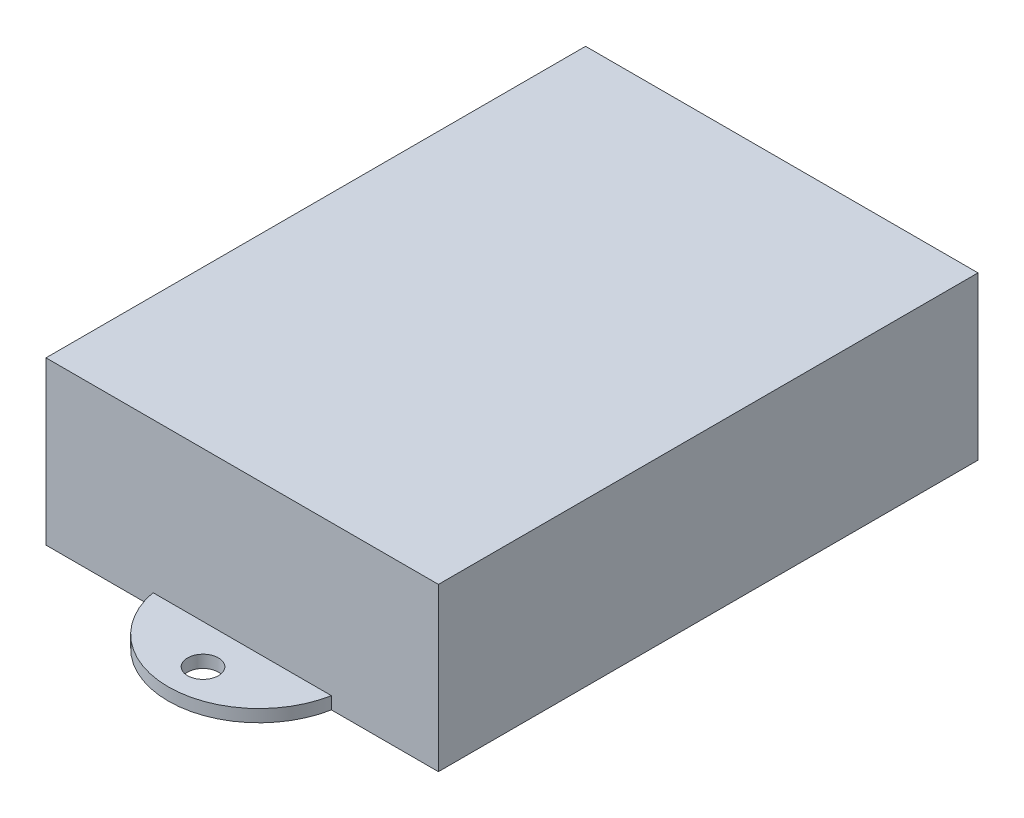
SolidWorks part; units mm, degrees
ref_plane "Front Plane" through (0, 0, 0) normal (0, 0, 1) x (1, 0, 0)
ref_plane "Top Plane" through (0, 0, 0) normal (0, 1, 0) x (1, 0, 0)
ref_plane "Right Plane" through (0, 0, 0) normal (1, 0, 0) x (0, 0, -1)
sketch "Sketch1" plane through (0, 0, 0) normal (0, 1, 0) x (1, 0, 0)
  line L1 (0, 0) -> (50.8, 0)
  line L2 (0, 0) -> (0, 69.85)
  line L3 (0, 69.85) -> (50.8, 69.85)
  line L4 (50.8, 0) -> (50.8, 69.85)
  dimension "D1" = 50.8
  dimension "D2" = 69.85
extrude "Boss-Extrude1" add sketch "Sketch1" along normal blind 21
sketch "Sketch2" plane through (0, 0, 0) normal (0, -1, 0) x (1, 0, 0)
  line L0 (25.4, 0) -> (25.4, -69.85) construction
  line L1 (0, 0) -> (50.8, 0) construction
  line L2 (50.8, -69.85) -> (0, -69.85) construction
  line L3 (25.4, -2.1787) -> (25.4, -67.6713) construction
  line L4 (37.1537, -2.1787) -> (37.1537, -67.6713)
  line L5 (13.6463, -2.1787) -> (13.6463, -67.6713)
  line L6 (25.4, 9.575) -> (25.4, -79.425) construction
  arc A0 (37.1537, -2.1787) -> (13.6463, -2.1787) centre (25.4, -2.1787) ccw
  arc A1 (13.6463, -67.6713) -> (37.1537, -67.6713) centre (25.4, -67.6713) ccw
  point P8 (25.4, -34.925)
  point P13 (13.85, 0)
  point P14 (36.95, 0)
  dimension "D1" = 23.1
  dimension "D2" = 89
extrude "Boss-Extrude2" add sketch "Sketch2" against normal blind 1.6
sketch "Sketch3" plane through (0, 1.6, 0) normal (0, 1, 0) x (1, 0, 0)
  line L0 (25.4, 74.925) -> (25.4, -5.075) construction
  line L1 (0, 34.925) -> (25.4, 34.925) construction
  line L2 (0, 69.85) -> (0, 0) construction
  line L3 (25.4, 34.925) -> (50.8, 34.925) construction
  line L4 (50.8, 0) -> (50.8, 69.85) construction
  circle A0 centre (25.4, 74.925) radius 2
  circle A1 centre (25.4, -5.075) radius 2
  dimension "D2" = 4
  dimension "D1" = 80
extrude "Cut-Extrude1" cut sketch "Sketch3" against normal through all
